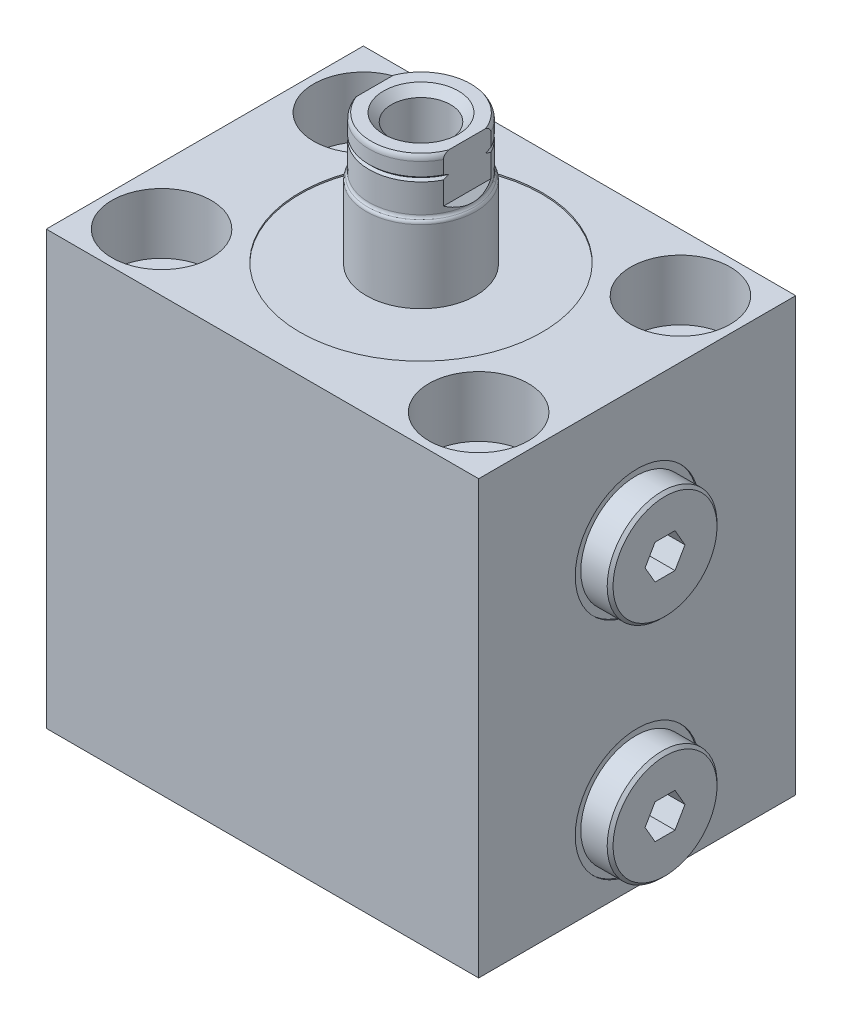
SolidWorks part; units mm, degrees
material "Alloy Steel"
ref_plane "Front Plane" through (0, 0, 0) normal (0, 0, 1) x (1, 0, 0)
ref_plane "Top Plane" through (0, 0, 0) normal (0, 1, 0) x (1, 0, 0)
ref_plane "Right Plane" through (0, 0, 0) normal (1, 0, 0) x (0, 0, -1)
sketch "Sketch1" plane through (0, 0, 0) normal (0, 1, 0) x (1, 0, 0)
  line L0 (-37.5, 27.5) -> (37.5, -27.5) construction
  line L1 (-37.5, 27.5) -> (37.5, 27.5)
  line L2 (-37.5, 27.5) -> (-37.5, -27.5)
  line L3 (-37.5, -27.5) -> (37.5, -27.5)
  line L4 (37.5, 27.5) -> (37.5, -27.5)
  point P4 (0, 0)
  dimension "D1" = 75
  dimension "D2" = 55
extrude "Extrude1" add sketch "Sketch1" along normal blind 75
sketch "Sketch2" plane through (0, 75, 0) normal (0, 1, 0) x (1, 0, 0)
  circle A0 centre (0, 0) radius 21
  dimension "D1" = 42
extrude "Cut-Extrude1" cut sketch "Sketch2" against normal blind 0.254
sketch "Sketch3" plane through (0, 0, 0) normal (0, 0, 1) x (1, 0, 0)
  line L0 (-6.848, 52) -> (35.4055, 52) construction
  line L1 (-37.5, 0) -> (37.5, 0) construction
  line L2 (37.5, 52) -> (37.5, 41.256)
  line L3 (37.5, 75) -> (37.5, 0) construction
  line L4 (37.5, 41.256) -> (37.246, 41.256)
  line L5 (37.246, 41.256) -> (37.246, 45.3452)
  line L6 (37.246, 45.3452) -> (36.5348, 46.0564)
  line L7 (36.5348, 46.0564) -> (21.752, 46.0564)
  line L8 (21.752, 46.0564) -> (21.752, 52)
  line L9 (21.752, 52) -> (37.5, 52)
  dimension "D1" = 52
  dimension "D2" = 21.488
  dimension "D3" = 0.254
  dimension "D4" = 11.8872
  dimension "D5" = 15.748
  dimension "D6" = 45
  dimension "D7" = 0.7112
revolve "Cut-Revolve1" cut sketch "Sketch3" angle 360 about L0
sketch "Sketch4" plane through (0, 0, 0) normal (0, 0, 1) x (1, 0, 0)
  line L0 (25.308, 52) -> (25.308, 57.9182)
  line L1 (36.5348, 52) -> (21.752, 52) construction
  line L2 (25.308, 57.9182) -> (37.246, 57.9182)
  line L3 (37.246, 57.9182) -> (37.246, 61.525)
  line L4 (37.246, 61.525) -> (42.326, 61.525)
  line L5 (42.326, 61.525) -> (42.326, 52)
  line L6 (42.326, 52) -> (25.308, 52)
  line L8 (37.246, 41.256) -> (37.246, 62.744) construction
  line L9 (8.7326, 52) -> (38.9701, 52) construction
  dimension "D1" = 11.938
  dimension "D2" = 11.8364
  dimension "D3" = 5.08
  dimension "D4" = 19.05
revolve "Revolve1" add sketch "Sketch4" angle 360 about L9
chamfer "Chamfer1" distance 0.508 angle 45 1 edges at (42.326, 52, 9.525)
sketch "Sketch5" plane through (42.326, 0, 0) normal (1, 0, 0) x (0, 0, -1)
  line L1 (1.7304, 54.9972) -> (-1.7304, 54.9972)
  line L2 (-1.7304, 54.9972) -> (-3.4609, 52)
  line L3 (-3.4609, 52) -> (-1.7304, 49.0028)
  line L4 (-1.7304, 49.0028) -> (1.7304, 49.0028)
  line L5 (1.7304, 49.0028) -> (3.4609, 52)
  line L6 (3.4609, 52) -> (1.7304, 54.9972)
  circle A0 centre (0, 52) radius 2.9972 construction
  dimension "D1" = 5.9944
extrude "Cut-Extrude2" cut sketch "Sketch5" against normal blind 5.9944
pattern_linear "LPattern1" count 2 spacing 39 along (0, -1, 0) of "Cut-Revolve1", "Revolve1", "Chamfer1", "Cut-Extrude2"
sketch "Sketch6" plane through (0, 0, 0) normal (0, 0, 1) x (1, 0, 0)
  line L0 (-37.5, 0) -> (37.5, 0) construction
  line L1 (0, 0) -> (0, 18.7888) construction
  line L12 (0, 0) -> (0, 14.8958)
  line L13 (5.7025, 0) -> (0, 0)
  line L14 (1.2446, 14.148) -> (0, 14.8958)
  line L15 (1.2446, 4.9529) -> (1.2446, 14.148)
  line L16 (1.7525, 4.445) -> (1.2446, 4.9529)
  line L17 (3.2512, 4.445) -> (1.7525, 4.445)
  line L18 (3.2512, 1.448) -> (3.2512, 4.445)
  line L19 (5.7025, 1.448) -> (3.2512, 1.448)
  line L20 (5.7025, 0) -> (5.7025, 1.448)
  dimension "D1" = 59
  dimension "D2" = 14.8958
  dimension "D3" = 2.4892
  dimension "D4" = 11.405
  dimension "D5" = 1.448
  dimension "D6" = 6.5024
  dimension "D7" = 4.445
  dimension "D8" = 45
  dimension "D9" = 0.5079
revolve "Cut-Revolve2" cut sketch "Sketch6" angle 360 about L1
sketch "Sketch7" plane through (0, 0, 0) normal (0, 0, 1) x (1, 0, 0)
  line L0 (0, 0) -> (0, 17.946) construction
  line L1 (0, 14.148) -> (0, 14.8958) construction
  line L2 (-37.5, 0) -> (37.5, 0) construction
  circle A0 centre (4.814, 0.5844) radius 0.889
  dimension "D1" = 9.628
  dimension "D2" = 1.778
  dimension "D3" = 0.5844
revolve "Revolve3" add sketch "Sketch7" angle 360 about L0
pattern_linear "LPattern2" count 2 spacing 27.5 along (-1, 0, 0) of "Cut-Revolve2", "Revolve3"
sketch "Sketch8" plane through (0, 0, 0) normal (0, 0, 1) x (1, 0, 0)
  line L0 (9.5, 74.746) -> (9.5, 87.3713)
  line L1 (8.6341, 97.5) -> (0, 97.5)
  line L2 (0, 97.5) -> (0, 74.746)
  line L3 (9, 96.5094) -> (9, 88.5)
  line L4 (9.5, 74.746) -> (0, 74.746)
  line L5 (0, 0) -> (0, 83.6966) construction
  line L6 (21, 74.746) -> (-21, 74.746) construction
  line L7 (-37.5, 0) -> (37.5, 0) construction
  arc A0 (9, 96.5094) -> (8.6341, 97.5) centre (7.476, 96.5094) ccw
  arc A1 (9, 88.5) -> (9.25, 87.9356) centre (9.762, 88.5) ccw
  arc A2 (9.5, 87.3713) -> (9.25, 87.9356) centre (8.738, 87.3713) ccw
  dimension "D1" = 1.524
  dimension "D7" = 0.762
  dimension "D8" = 0.762
  dimension "D2" = 9
  dimension "D3" = 97.5
  dimension "D4" = 0.9906
  dimension "D5" = 18
  dimension "D6" = 19
revolve "Revolve4" add sketch "Sketch8" angle 360 about L5
sketch "Sketch10" plane through (0, 0, 0) normal (0, 0, 1) x (1, 0, 0)
  line L0 (6.5, 97.5) -> (5.131, 96.131)
  line L1 (5.131, 96.131) -> (5.131, 77.18)
  line L2 (5.131, 77.18) -> (0, 74.097)
  line L3 (0, 74.097) -> (0, 97.5)
  line L4 (0, 97.5) -> (6.5, 97.5)
  line L5 (0, 97.5) -> (0, 82.7828) construction
  line L6 (8.6341, 97.5) -> (-8.6341, 97.5) construction
  dimension "D1" = 45
  dimension "D2" = 1.369
  dimension "D3" = 10.262
  dimension "D4" = 59
  dimension "D5" = 20.32
revolve "Cut-Revolve3" cut sketch "Sketch10" angle 360 about L5
sketch "Sketch11" plane through (0, 0, 0) normal (0, 0, 1) x (1, 0, 0)
  line L0 (9, 94.198) -> (8.619, 93.817)
  line L1 (8.619, 93.817) -> (9, 93.436)
  line L2 (9, 93.436) -> (9, 94.198)
  line L3 (9, 88.5) -> (9, 96.5094) construction
  line L4 (8.619, 93.817) -> (9, 93.817) construction
  line L5 (8.6341, 97.5) -> (-8.6341, 97.5) construction
  line L6 (0, 0) -> (0, 94.5745) construction
  dimension "D1" = 0.762
  dimension "D2" = 3.683
  dimension "D3" = 90
revolve "Cut-Revolve4" cut sketch "Sketch11" angle 360 about L6
sketch "Sketch12" plane through (0, 0, 0) normal (0, 0, 1) x (1, 0, 0)
  line L0 (0, 0) -> (0, 87.4273) construction
  line L1 (8, 97.5) -> (8, 89.5)
  line L2 (6.5, 97.5) -> (-6.5, 97.5) construction
  line L3 (8, 89.5) -> (9.5, 88)
  line L4 (9.5, 88) -> (9.5, 97.5)
  line L5 (9.5, 97.5) -> (8, 97.5)
  line L6 (9.5, 74.746) -> (9.5, 87.3713) construction
  line L7 (-9.5, 97.5) -> (-8, 97.5)
  line L8 (-9.5, 88) -> (-9.5, 97.5)
  line L9 (-8, 89.5) -> (-9.5, 88)
  line L10 (-8, 97.5) -> (-8, 89.5)
  dimension "D1" = 16
  dimension "D2" = 45
  dimension "D3" = 8
extrude "Cut-Extrude3" cut sketch "Sketch12" against normal through all and the other way through all
hole_wizard "Hole1" positions "Sketch14" profile "Sketch13" legacy end condition through all
sketch "Sketch14" plane through (0, 75, 0) normal (0, 1, 0) x (-1, 0, 0)
  line L0 (0, 0) -> (0, 30.0241) construction
  line L1 (0, 0) -> (32.2854, 0) construction
  point P0 (27.5, 17.5)
  point P10 (27.5, -17.5)
  point P12 (-27.5, -17.5)
  point P13 (-27.5, 17.5)
  dimension "D1" = 35
  dimension "D2" = 55
sketch "Sketch13" plane through (-27.5, 75, 17.5) normal (1, 0, 0) x (0, 0, 1)
  line L0 (0, 0) -> (0, 75.3046)
  line L1 (0, 75.3046) -> (5.245, 75.3046)
  line L2 (5.245, 75.3046) -> (5.245, 10.49)
  line L3 (5.245, 10.49) -> (8.6235, 10.49)
  line L4 (8.6235, 10.49) -> (8.6235, 0)
  line L5 (8.6235, 0) -> (0, 0)
  line L6 (0, 110) -> (0, -10) construction
  dimension "Diameter" = 10.49
  dimension "Depth" = 75.3046
  dimension "C-Bore Diameter" = 17.247
  dimension "C-Bore Depth" = 10.49
